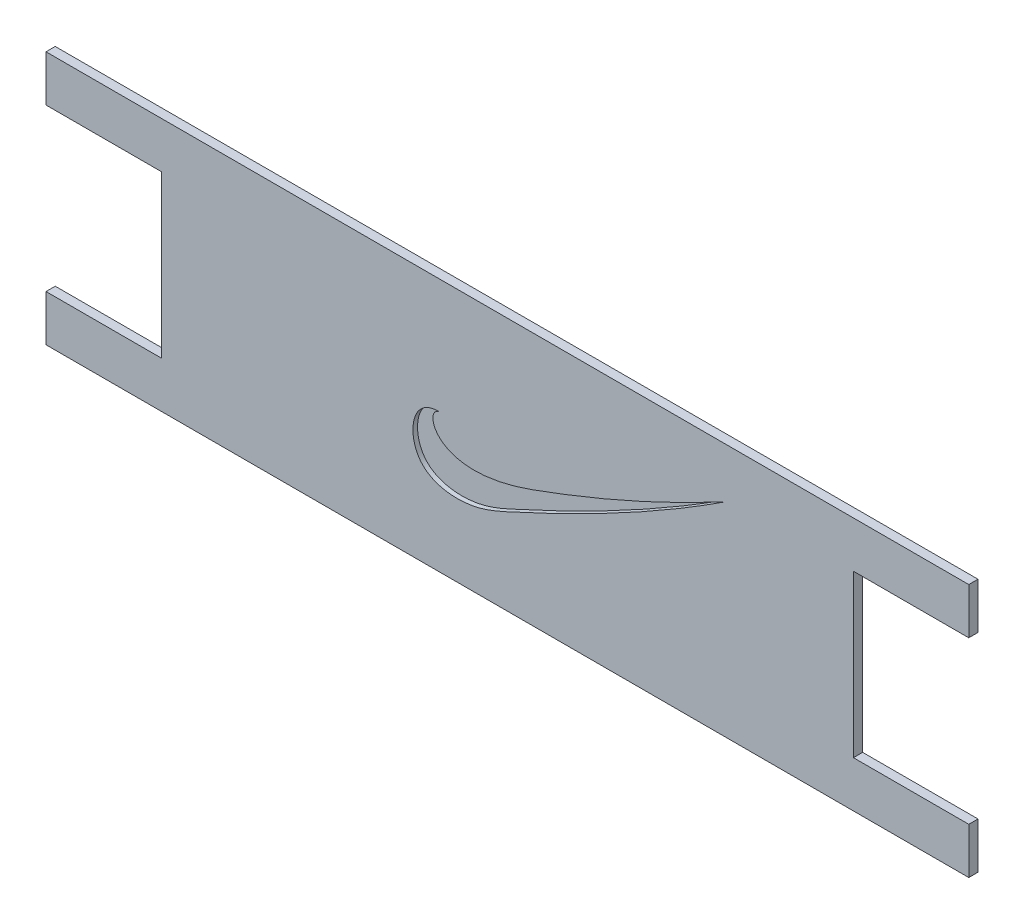
SolidWorks part; units mm, degrees
ref_plane "Front Plane" through (0, 0, 0) normal (0, 0, 1) x (1, 0, 0)
ref_plane "Top Plane" through (0, 0, 0) normal (0, 1, 0) x (1, 0, 0)
ref_plane "Right Plane" through (0, 0, 0) normal (1, 0, 0) x (0, 0, -1)
sketch "Sketch1" plane through (0, 0, 0) normal (0, 0, 1) x (1, 0, 0)
  line L1 (-48.3108, 14.244) -> (151.6892, 14.244)
  line L2 (-48.3108, 14.244) -> (-48.3108, 4.244)
  line L3 (-48.3108, -40.756) -> (151.6892, -40.756)
  line L4 (151.6892, 14.244) -> (151.6892, 4.244)
  line L5 (-23.3108, 4.244) -> (-48.3108, 4.244)
  line L6 (-48.3108, -30.756) -> (-23.3108, -30.756)
  line L9 (126.6892, 4.244) -> (151.6892, 4.244)
  line L10 (-23.3108, 4.244) -> (-23.3108, -30.756)
  line L11 (-48.3108, -30.756) -> (-48.3108, -40.756)
  line L13 (126.6892, -30.756) -> (151.6892, -30.756)
  line L14 (126.6892, 4.244) -> (126.6892, -30.756)
  line L15 (151.6892, -30.756) -> (151.6892, -40.756)
  dimension "D1" = 55
  dimension "D2" = 200
  dimension "D3" = 10
  dimension "D5" = 10
extrude "Boss-Extrude1" add sketch "Sketch1" along normal blind 2
sketch "Sketch3" plane through (0, 0, 2) normal (0, 0, 1) x (1, 0, 0)
  line L1 (51.6892, 36.8392) -> (51.6892, -73.5664) construction
  spline S0 degree 3 poles (37.1895, -10.7183) (33.4742, -10.6242) (35.3006, -23.2165) (74.22, -9.0463) (87.6649, -2.595) (98.8534, 3.3374) knots 0 0 0 0 0.517765 0.59262 1 1 1 1
  spline S1 degree 3 poles (37.1895, -10.7183) (30.8159, -10.3327) (29.1569, -24.1699) (43.2502, -25.8533) (65.1902, -16.1789) (83.9965, -6.3848) (98.8534, 3.3374) knots 0 0 0 0 0.163171 0.291764 0.388322 1 1 1 1
  point P7 (56.8218, -21.6508)
  point P11 (40.2723, 1.9266)
  point P13 (31.8842, -13.7161)
  point P15 (35.0581, -4.8746)
  point P17 (59.0889, -13.7161)
  point P18 (0, 0)
  point P19 (83.1196, -3.9678)
  point P20 (83.1196, -6.2348)
  point P21 (54.5547, -21.4241)
  point P22 (86.7469, -1.7007)
  point P23 (43.6729, -24.8247)
  point P24 (32.791, -21.8775)
  point P25 (38.0052, -8.2752)
  point P26 (0, 0)
  point P27 (97.8555, 3.9669)
  point P28 (51.6892, -22.1042)
  point P29 (0, 0)
  point P30 (36.1916, -10.0888)
  point P31 (0, 0)
  point P32 (57.7105, -15.0351)
  dimension "D1" = 100
extrude "Cut-Extrude1" cut sketch "Sketch3" against normal blind 1
